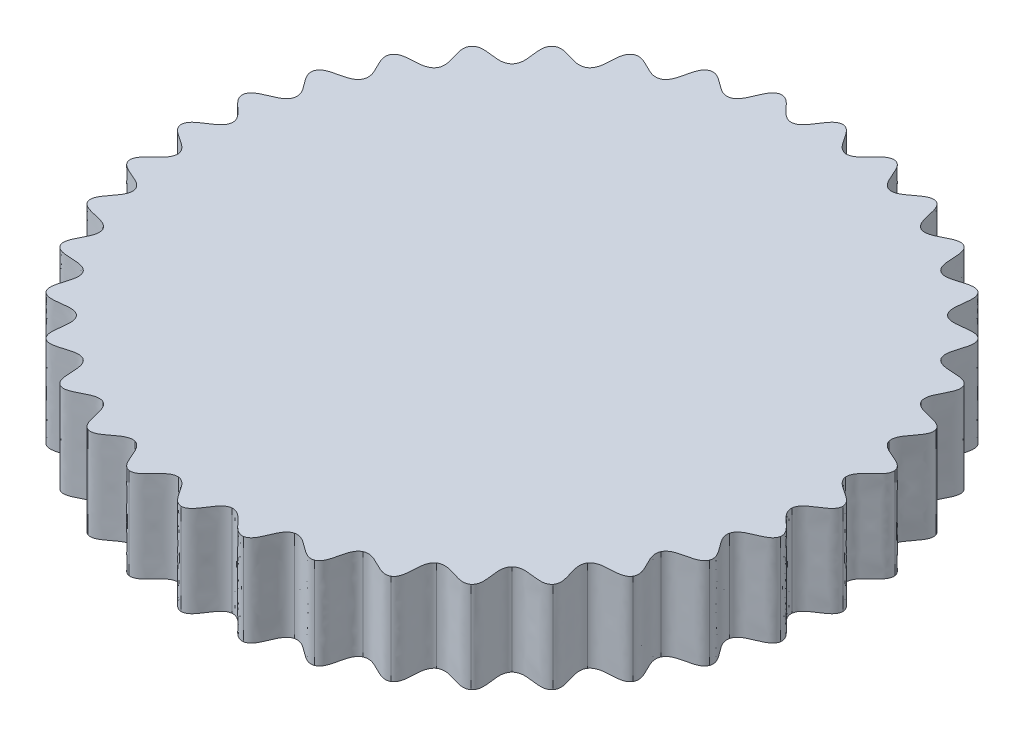
SolidWorks part; units mm, degrees
ref_plane "Front Plane" through (0, 0, 0) normal (0, 0, 1) x (1, 0, 0)
ref_plane "Top Plane" through (0, 0, 0) normal (0, 1, 0) x (1, 0, 0)
ref_plane "Right Plane" through (0, 0, 0) normal (1, 0, 0) x (0, 0, -1)
sketch "Sketch1" plane through (0, 0, 0) normal (0, 1, 0) x (1, 0, 0)
  line L0 (0, 0) -> (0, 72.5) construction
  line L1 (0, 0) -> (6.3188, 72.2241) construction
  line L2 (6.3188, 72.2241) -> (5.883, 67.2431) construction
  line L3 (0, 72.5) -> (5.883, 67.2431) construction
  circle A0 centre (0, 0) radius 72.5 construction
  spline S0 degree 3 poles (0, 72.5) (1.3147, 72.4754) (2.9372, 69.8075) (4.577, 67.3958) (5.883, 67.2431) knots 0 0 0 0 0.5 1 1 1 1
  spline S1 degree 3 poles (0, 72.5) (-1.3147, 72.4754) (-2.9372, 69.8075) (-4.577, 67.3958) (-5.883, 67.2431) knots 0 0 0 0 0.5 1 1 1 1
  spline S2 degree 3 poles (12.5895, 71.3986) (11.2905, 71.6027) (9.2294, 69.257) (7.1957, 67.1667) (5.883, 67.2431) knots 0 0 0 0 0.5 1 1 1 1
  spline S3 degree 3 poles (12.5895, 71.3986) (13.8799, 71.1461) (15.0145, 68.2369) (16.2106, 65.5772) (17.4703, 65.2) knots 0 0 0 0 0.5 1 1 1 1
  spline S4 degree 3 poles (24.7965, 68.1277) (23.5527, 68.5543) (21.1155, 66.6022) (18.7498, 64.8968) (17.4703, 65.2) knots 0 0 0 0 0.5 1 1 1 1
  spline S5 degree 3 poles (24.7965, 68.1277) (26.0235, 67.655) (26.6356, 64.593) (27.3517, 61.7659) (28.5267, 61.1758) knots 0 0 0 0 0.5 1 1 1 1
  spline S6 degree 3 poles (36.25, 62.7868) (35.0992, 63.4229) (32.3601, 61.9237) (29.7341, 60.655) (28.5267, 61.1758) knots 0 0 0 0 0.5 1 1 1 1
  spline S7 degree 3 poles (36.25, 62.7868) (37.3763, 62.1082) (37.4474, 58.9865) (37.6617, 56.078) (38.7164, 55.2928) knots 0 0 0 0 0.5 1 1 1 1
  spline S8 degree 3 poles (46.6021, 55.5382) (45.5792, 56.3645) (42.6214, 55.3636) (39.815, 54.5702) (38.7164, 55.2928) knots 0 0 0 0 0.5 1 1 1 1
  spline S9 degree 3 poles (46.6021, 55.5382) (47.5934, 54.6743) (47.1214, 51.5877) (46.8274, 48.6862) (47.7297, 47.7297) knots 0 0 0 0 0.5 1 1 1 1
  spline S10 degree 3 poles (55.5382, 46.6021) (54.6743, 47.5934) (51.5877, 47.1214) (48.6862, 46.8274) (47.7297, 47.7297) knots 0 0 0 0 0.5 1 1 1 1
  spline S11 degree 3 poles (55.5382, 46.6021) (56.3645, 45.5792) (55.3636, 42.6214) (54.5702, 39.815) (55.2928, 38.7164) knots 0 0 0 0 0.5 1 1 1 1
  spline S12 degree 3 poles (62.7868, 36.25) (62.1082, 37.3763) (58.9865, 37.4474) (56.078, 37.6617) (55.2928, 38.7164) knots 0 0 0 0 0.5 1 1 1 1
  spline S13 degree 3 poles (62.7868, 36.25) (63.4229, 35.0992) (61.9237, 32.3601) (60.655, 29.7341) (61.1758, 28.5267) knots 0 0 0 0 0.5 1 1 1 1
  spline S14 degree 3 poles (68.1277, 24.7965) (67.655, 26.0235) (64.593, 26.6356) (61.7659, 27.3517) (61.1758, 28.5267) knots 0 0 0 0 0.5 1 1 1 1
  spline S15 degree 3 poles (68.1277, 24.7965) (68.5543, 23.5527) (66.6022, 21.1155) (64.8968, 18.7498) (65.2, 17.4703) knots 0 0 0 0 0.5 1 1 1 1
  spline S16 degree 3 poles (71.3986, 12.5895) (71.1461, 13.8799) (68.2369, 15.0145) (65.5772, 16.2106) (65.2, 17.4703) knots 0 0 0 0 0.5 1 1 1 1
  spline S17 degree 3 poles (71.3986, 12.5895) (71.6027, 11.2905) (69.257, 9.2294) (67.1667, 7.1957) (67.2431, 5.883) knots 0 0 0 0 0.5 1 1 1 1
  spline S18 degree 3 poles (72.5, 0) (72.4754, 1.3147) (69.8075, 2.9372) (67.3958, 4.577) (67.2431, 5.883) knots 0 0 0 0 0.5 1 1 1 1
  spline S19 degree 3 poles (72.5, 0) (72.4754, -1.3147) (69.8075, -2.9372) (67.3958, -4.577) (67.2431, -5.883) knots 0 0 0 0 0.5 1 1 1 1
  spline S20 degree 3 poles (71.3986, -12.5895) (71.6027, -11.2905) (69.257, -9.2294) (67.1667, -7.1957) (67.2431, -5.883) knots 0 0 0 0 0.5 1 1 1 1
  spline S21 degree 3 poles (71.3986, -12.5895) (71.1461, -13.8799) (68.2369, -15.0145) (65.5772, -16.2106) (65.2, -17.4703) knots 0 0 0 0 0.5 1 1 1 1
  spline S22 degree 3 poles (68.1277, -24.7965) (68.5543, -23.5527) (66.6022, -21.1155) (64.8968, -18.7498) (65.2, -17.4703) knots 0 0 0 0 0.5 1 1 1 1
  spline S23 degree 3 poles (68.1277, -24.7965) (67.655, -26.0235) (64.593, -26.6356) (61.7659, -27.3517) (61.1758, -28.5267) knots 0 0 0 0 0.5 1 1 1 1
  spline S24 degree 3 poles (62.7868, -36.25) (63.4229, -35.0992) (61.9237, -32.3601) (60.655, -29.7341) (61.1758, -28.5267) knots 0 0 0 0 0.5 1 1 1 1
  spline S25 degree 3 poles (62.7868, -36.25) (62.1082, -37.3763) (58.9865, -37.4474) (56.078, -37.6617) (55.2928, -38.7164) knots 0 0 0 0 0.5 1 1 1 1
  spline S26 degree 3 poles (55.5382, -46.6021) (56.3645, -45.5792) (55.3636, -42.6214) (54.5702, -39.815) (55.2928, -38.7164) knots 0 0 0 0 0.5 1 1 1 1
  spline S27 degree 3 poles (55.5382, -46.6021) (54.6743, -47.5934) (51.5877, -47.1214) (48.6862, -46.8274) (47.7297, -47.7297) knots 0 0 0 0 0.5 1 1 1 1
  spline S28 degree 3 poles (46.6021, -55.5382) (47.5934, -54.6743) (47.1214, -51.5877) (46.8274, -48.6862) (47.7297, -47.7297) knots 0 0 0 0 0.5 1 1 1 1
  spline S29 degree 3 poles (46.6021, -55.5382) (45.5792, -56.3645) (42.6214, -55.3636) (39.815, -54.5702) (38.7164, -55.2928) knots 0 0 0 0 0.5 1 1 1 1
  spline S30 degree 3 poles (36.25, -62.7868) (37.3763, -62.1082) (37.4474, -58.9865) (37.6617, -56.078) (38.7164, -55.2928) knots 0 0 0 0 0.5 1 1 1 1
  spline S31 degree 3 poles (36.25, -62.7868) (35.0992, -63.4229) (32.3601, -61.9237) (29.7341, -60.655) (28.5267, -61.1758) knots 0 0 0 0 0.5 1 1 1 1
  spline S32 degree 3 poles (24.7965, -68.1277) (26.0235, -67.655) (26.6356, -64.593) (27.3517, -61.7659) (28.5267, -61.1758) knots 0 0 0 0 0.5 1 1 1 1
  spline S33 degree 3 poles (24.7965, -68.1277) (23.5527, -68.5543) (21.1155, -66.6022) (18.7498, -64.8968) (17.4703, -65.2) knots 0 0 0 0 0.5 1 1 1 1
  spline S34 degree 3 poles (12.5895, -71.3986) (13.8799, -71.1461) (15.0145, -68.2369) (16.2106, -65.5772) (17.4703, -65.2) knots 0 0 0 0 0.5 1 1 1 1
  spline S35 degree 3 poles (12.5895, -71.3986) (11.2905, -71.6027) (9.2294, -69.257) (7.1957, -67.1667) (5.883, -67.2431) knots 0 0 0 0 0.5 1 1 1 1
  spline S36 degree 3 poles (0, -72.5) (1.3147, -72.4754) (2.9372, -69.8075) (4.577, -67.3958) (5.883, -67.2431) knots 0 0 0 0 0.5 1 1 1 1
  spline S37 degree 3 poles (0, -72.5) (-1.3147, -72.4754) (-2.9372, -69.8075) (-4.577, -67.3958) (-5.883, -67.2431) knots 0 0 0 0 0.5 1 1 1 1
  spline S38 degree 3 poles (-12.5895, -71.3986) (-11.2905, -71.6027) (-9.2294, -69.257) (-7.1957, -67.1667) (-5.883, -67.2431) knots 0 0 0 0 0.5 1 1 1 1
  spline S39 degree 3 poles (-12.5895, -71.3986) (-13.8799, -71.1461) (-15.0145, -68.2369) (-16.2106, -65.5772) (-17.4703, -65.2) knots 0 0 0 0 0.5 1 1 1 1
  spline S40 degree 3 poles (-24.7965, -68.1277) (-23.5527, -68.5543) (-21.1155, -66.6022) (-18.7498, -64.8968) (-17.4703, -65.2) knots 0 0 0 0 0.5 1 1 1 1
  spline S41 degree 3 poles (-24.7965, -68.1277) (-26.0235, -67.655) (-26.6356, -64.593) (-27.3517, -61.7659) (-28.5267, -61.1758) knots 0 0 0 0 0.5 1 1 1 1
  spline S42 degree 3 poles (-36.25, -62.7868) (-35.0992, -63.4229) (-32.3601, -61.9237) (-29.7341, -60.655) (-28.5267, -61.1758) knots 0 0 0 0 0.5 1 1 1 1
  spline S43 degree 3 poles (-36.25, -62.7868) (-37.3763, -62.1082) (-37.4474, -58.9865) (-37.6617, -56.078) (-38.7164, -55.2928) knots 0 0 0 0 0.5 1 1 1 1
  spline S44 degree 3 poles (-46.6021, -55.5382) (-45.5792, -56.3645) (-42.6214, -55.3636) (-39.815, -54.5702) (-38.7164, -55.2928) knots 0 0 0 0 0.5 1 1 1 1
  spline S45 degree 3 poles (-46.6021, -55.5382) (-47.5934, -54.6743) (-47.1214, -51.5877) (-46.8274, -48.6862) (-47.7297, -47.7297) knots 0 0 0 0 0.5 1 1 1 1
  spline S46 degree 3 poles (-55.5382, -46.6021) (-54.6743, -47.5934) (-51.5877, -47.1214) (-48.6862, -46.8274) (-47.7297, -47.7297) knots 0 0 0 0 0.5 1 1 1 1
  spline S47 degree 3 poles (-55.5382, -46.6021) (-56.3645, -45.5792) (-55.3636, -42.6214) (-54.5702, -39.815) (-55.2928, -38.7164) knots 0 0 0 0 0.5 1 1 1 1
  spline S48 degree 3 poles (-62.7868, -36.25) (-62.1082, -37.3763) (-58.9865, -37.4474) (-56.078, -37.6617) (-55.2928, -38.7164) knots 0 0 0 0 0.5 1 1 1 1
  spline S49 degree 3 poles (-62.7868, -36.25) (-63.4229, -35.0992) (-61.9237, -32.3601) (-60.655, -29.7341) (-61.1758, -28.5267) knots 0 0 0 0 0.5 1 1 1 1
  spline S50 degree 3 poles (-68.1277, -24.7965) (-67.655, -26.0235) (-64.593, -26.6356) (-61.7659, -27.3517) (-61.1758, -28.5267) knots 0 0 0 0 0.5 1 1 1 1
  spline S51 degree 3 poles (-68.1277, -24.7965) (-68.5543, -23.5527) (-66.6022, -21.1155) (-64.8968, -18.7498) (-65.2, -17.4703) knots 0 0 0 0 0.5 1 1 1 1
  spline S52 degree 3 poles (-71.3986, -12.5895) (-71.1461, -13.8799) (-68.2369, -15.0145) (-65.5772, -16.2106) (-65.2, -17.4703) knots 0 0 0 0 0.5 1 1 1 1
  spline S53 degree 3 poles (-71.3986, -12.5895) (-71.6027, -11.2905) (-69.257, -9.2294) (-67.1667, -7.1957) (-67.2431, -5.883) knots 0 0 0 0 0.5 1 1 1 1
  spline S54 degree 3 poles (-72.5, 0) (-72.4754, -1.3147) (-69.8075, -2.9372) (-67.3958, -4.577) (-67.2431, -5.883) knots 0 0 0 0 0.5 1 1 1 1
  spline S55 degree 3 poles (-72.5, 0) (-72.4754, 1.3147) (-69.8075, 2.9372) (-67.3958, 4.577) (-67.2431, 5.883) knots 0 0 0 0 0.5 1 1 1 1
  spline S56 degree 3 poles (-71.3986, 12.5895) (-71.6027, 11.2905) (-69.257, 9.2294) (-67.1667, 7.1957) (-67.2431, 5.883) knots 0 0 0 0 0.5 1 1 1 1
  spline S57 degree 3 poles (-71.3986, 12.5895) (-71.1461, 13.8799) (-68.2369, 15.0145) (-65.5772, 16.2106) (-65.2, 17.4703) knots 0 0 0 0 0.5 1 1 1 1
  spline S58 degree 3 poles (-68.1277, 24.7965) (-68.5543, 23.5527) (-66.6022, 21.1155) (-64.8968, 18.7498) (-65.2, 17.4703) knots 0 0 0 0 0.5 1 1 1 1
  spline S59 degree 3 poles (-68.1277, 24.7965) (-67.655, 26.0235) (-64.593, 26.6356) (-61.7659, 27.3517) (-61.1758, 28.5267) knots 0 0 0 0 0.5 1 1 1 1
  spline S60 degree 3 poles (-62.7868, 36.25) (-63.4229, 35.0992) (-61.9237, 32.3601) (-60.655, 29.7341) (-61.1758, 28.5267) knots 0 0 0 0 0.5 1 1 1 1
  spline S61 degree 3 poles (-62.7868, 36.25) (-62.1082, 37.3763) (-58.9865, 37.4474) (-56.078, 37.6617) (-55.2928, 38.7164) knots 0 0 0 0 0.5 1 1 1 1
  spline S62 degree 3 poles (-55.5382, 46.6021) (-56.3645, 45.5792) (-55.3636, 42.6214) (-54.5702, 39.815) (-55.2928, 38.7164) knots 0 0 0 0 0.5 1 1 1 1
  spline S63 degree 3 poles (-55.5382, 46.6021) (-54.6743, 47.5934) (-51.5877, 47.1214) (-48.6862, 46.8274) (-47.7297, 47.7297) knots 0 0 0 0 0.5 1 1 1 1
  spline S64 degree 3 poles (-46.6021, 55.5382) (-47.5934, 54.6743) (-47.1214, 51.5877) (-46.8274, 48.6862) (-47.7297, 47.7297) knots 0 0 0 0 0.5 1 1 1 1
  spline S65 degree 3 poles (-46.6021, 55.5382) (-45.5792, 56.3645) (-42.6214, 55.3636) (-39.815, 54.5702) (-38.7164, 55.2928) knots 0 0 0 0 0.5 1 1 1 1
  spline S66 degree 3 poles (-36.25, 62.7868) (-37.3763, 62.1082) (-37.4474, 58.9865) (-37.6617, 56.078) (-38.7164, 55.2928) knots 0 0 0 0 0.5 1 1 1 1
  spline S67 degree 3 poles (-36.25, 62.7868) (-35.0992, 63.4229) (-32.3601, 61.9237) (-29.7341, 60.655) (-28.5267, 61.1758) knots 0 0 0 0 0.5 1 1 1 1
  spline S68 degree 3 poles (-24.7965, 68.1277) (-26.0235, 67.655) (-26.6356, 64.593) (-27.3517, 61.7659) (-28.5267, 61.1758) knots 0 0 0 0 0.5 1 1 1 1
  spline S69 degree 3 poles (-24.7965, 68.1277) (-23.5527, 68.5543) (-21.1155, 66.6022) (-18.7498, 64.8968) (-17.4703, 65.2) knots 0 0 0 0 0.5 1 1 1 1
  spline S70 degree 3 poles (-12.5895, 71.3986) (-13.8799, 71.1461) (-15.0145, 68.2369) (-16.2106, 65.5772) (-17.4703, 65.2) knots 0 0 0 0 0.5 1 1 1 1
  spline S71 degree 3 poles (-12.5895, 71.3986) (-11.2905, 71.6027) (-9.2294, 69.257) (-7.1957, 67.1667) (-5.883, 67.2431) knots 0 0 0 0 0.5 1 1 1 1
  point P7 (2.9415, 69.8716)
  point P187 (0, 0)
  dimension "D1" = 5
  dimension "D3" = 145
  dimension "D2" = 5
extrude "Boss-Extrude1" add sketch "Sketch1" along normal blind 20
